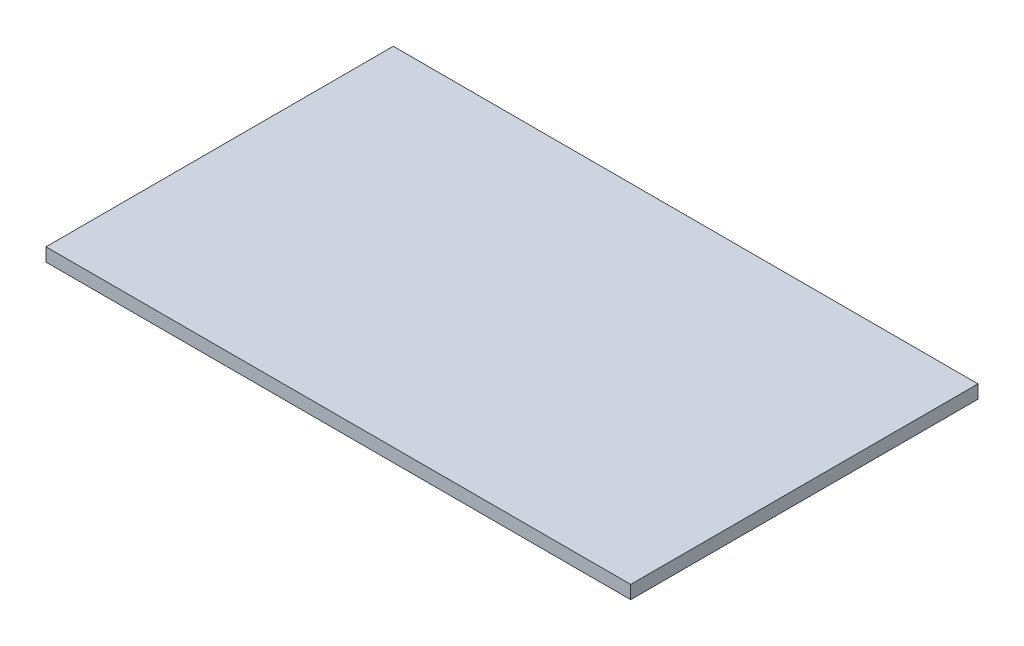
SolidWorks part; units mm, degrees
ref_plane "Front Plane" through (0, 0, 0) normal (0, 0, 1) x (1, 0, 0)
ref_plane "Top Plane" through (0, 0, 0) normal (0, 1, 0) x (1, 0, 0)
ref_plane "Right Plane" through (0, 0, 0) normal (1, 0, 0) x (0, 0, -1)
sketch "Sketch1" plane through (0, 0, 0) normal (0, 1, 0) x (1, 0, 0)
  line L1 (0, 0) -> (1676.4, 0)
  line L2 (0, 0) -> (0, 995.68)
  line L3 (0, 995.68) -> (1676.4, 995.68)
  line L4 (1676.4, 0) -> (1676.4, 995.68)
  dimension "D1" = 1676.4
  dimension "D2" = 995.68
extrude "Boss-Extrude1" add sketch "Sketch1" along normal blind 38.1
